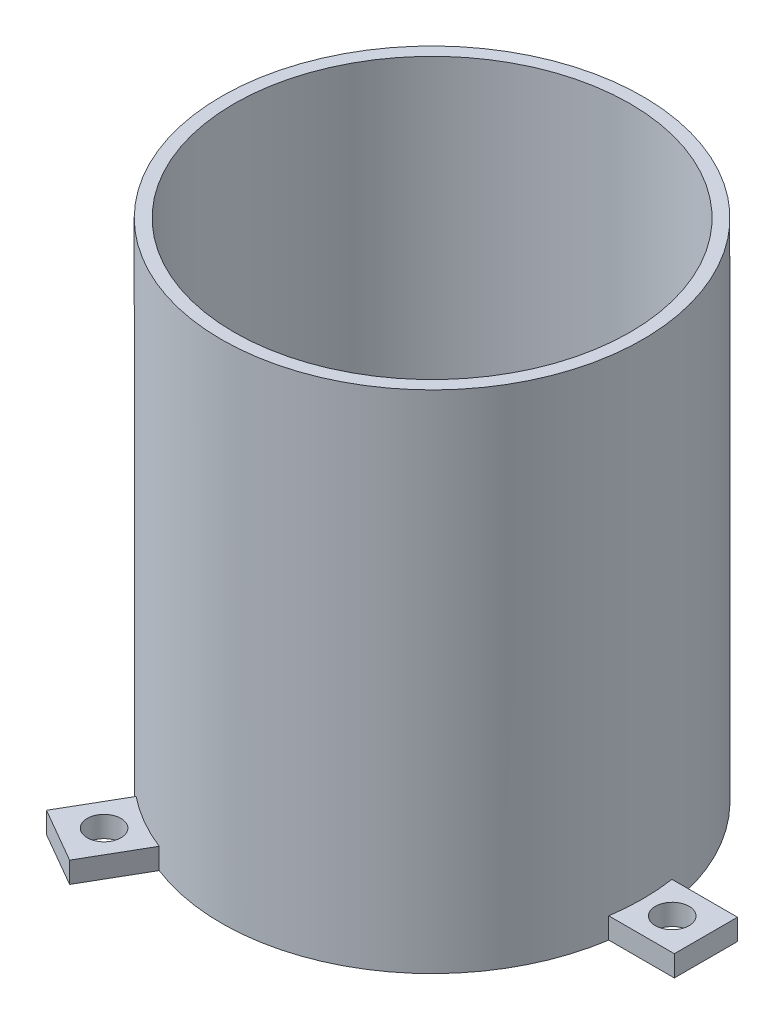
SolidWorks part; units mm, degrees
ref_plane "Front Plane" through (0, 0, 0) normal (0, 0, 1) x (1, 0, 0)
ref_plane "Top Plane" through (0, 0, 0) normal (0, 1, 0) x (1, 0, 0)
ref_plane "Right Plane" through (0, 0, 0) normal (1, 0, 0) x (0, 0, -1)
sketch "Sketch1" plane through (0, 0, 0) normal (0, 1, 0) x (1, 0, 0)
  circle A0 centre (0, 0) radius 50
  dimension "D1" = 100
extrude "Boss-Extrude1" add sketch "Sketch1" along normal blind 120
shell "Shell1" thickness 3
sketch "Sketch2" plane through (0, 0, 0) normal (0, -1, 0) x (1, 0, 0)
  line L0 (50, 0) -> (69.9437, 0) construction
  line L1 (49.4343, 7.5) -> (65, 7.5)
  line L2 (65, 7.5) -> (65, -7.5)
  line L3 (65, -7.5) -> (49.4343, -7.5)
  line L4 (-18.222, -46.5614) -> (-26.0048, -60.0417)
  line L5 (-26.0048, -60.0417) -> (-38.9952, -52.5417)
  line L6 (-38.9952, -52.5417) -> (-31.2123, -39.0614)
  line L7 (-31.2123, 39.0614) -> (-38.9952, 52.5417)
  line L8 (-38.9952, 52.5417) -> (-26.0048, 60.0417)
  line L9 (-26.0048, 60.0417) -> (-18.222, 46.5614)
  circle A0 centre (0, 0) radius 50 construction
  arc A1 (49.4343, -7.5) -> (49.4343, 7.5) centre (0, 0) ccw
  circle A2 centre (57, 0) radius 4
  circle A3 centre (-28.5, -49.3634) radius 4
  arc A4 (-31.2123, -39.0614) -> (-18.222, -46.5614) centre (0, 0) ccw
  circle A5 centre (-28.5, 49.3634) radius 4
  arc A6 (-18.222, 46.5614) -> (-31.2123, 39.0614) centre (0, 0) ccw
  dimension "D4" = 8
  dimension "D1" = 7.5
  dimension "D2" = 7.5
  dimension "D3" = 15
  dimension "D5" = 8
  dimension "D6" = 3
extrude "Boss-Extrude2" add sketch "Sketch2" against normal blind 5
